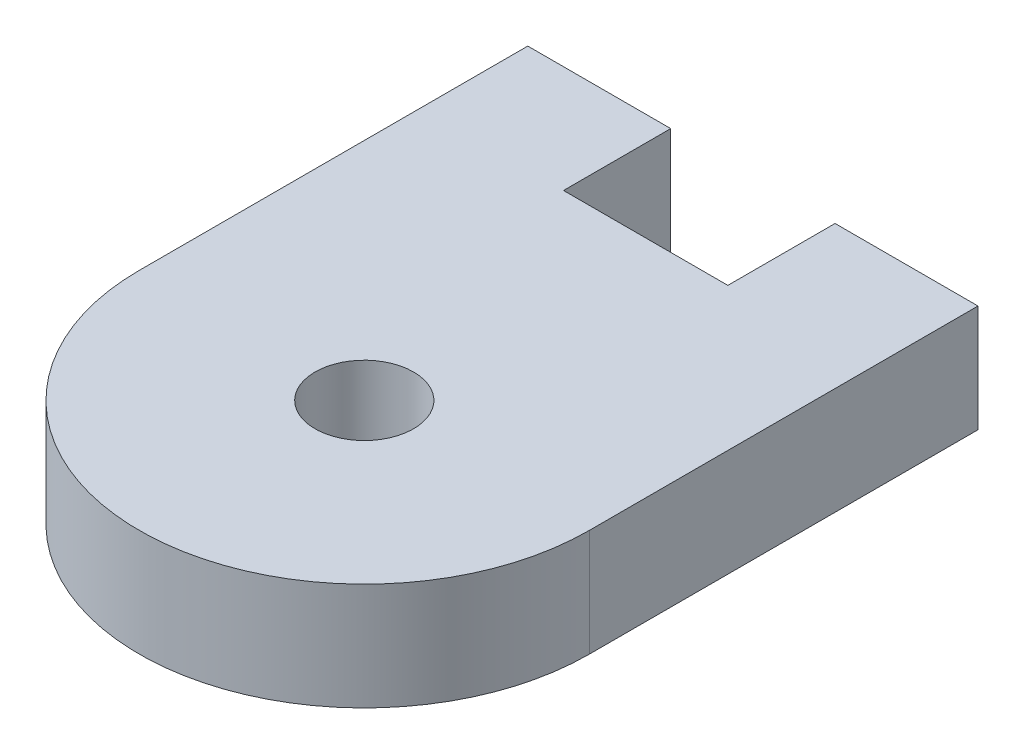
SolidWorks part; units mm, degrees
ref_plane "Front Plane" through (0, 0, 0) normal (0, 0, 1) x (1, 0, 0)
ref_plane "Top Plane" through (0, 0, 0) normal (0, 1, 0) x (1, 0, 0)
ref_plane "Right Plane" through (0, 0, 0) normal (1, 0, 0) x (0, 0, -1)
sketch "Sketch1" plane through (0, 0, 0) normal (0, 1, 0) x (1, 0, 0)
  line L1 (0, 0) -> (32, 0)
  line L2 (0, 0) -> (0, 20)
  line L3 (0, 20) -> (32, 20)
  line L4 (32, 0) -> (32, 20)
  arc A0 (0, 0) -> (32, 0) centre (16, 0) ccw
  dimension "D1" = 20
  dimension "D2" = 32
extrude "Boss-Extrude1" add sketch "Sketch1" along normal blind 7.62 contours L2 L3 L4 A0
sketch "Sketch2" plane through (0, 0, 0) normal (0, -1, 0) x (1, 0, 0)
  line L0 (32, 0) -> (0, 0) construction
  circle A0 centre (16, 0) radius 3.5
extrude "Cut-Extrude1" cut sketch "Sketch2" against normal through all
sketch "Sketch3" plane through (0, 0, -20) normal (0, 0, -1) x (-1, 0, 0)
  line L0 (0, 0) -> (-32, 0) construction
  line L1 (-32, 7.62) -> (-21.84, 7.62)
  line L2 (-32, 7.62) -> (-32, 0)
  line L3 (-32, 0) -> (-21.84, 0)
  line L4 (-21.84, 7.62) -> (-21.84, 0)
  line L6 (0, 7.62) -> (-10.16, 7.62)
  line L7 (0, 7.62) -> (0, 0)
  line L8 (0, 0) -> (-10.16, 0)
  line L9 (-10.16, 7.62) -> (-10.16, 0)
  dimension "D1" = 10.16
  dimension "D2" = 10.16
  dimension "D3" = 11.68
extrude "Boss-Extrude2" add sketch "Sketch3" along normal blind 7.62
equation "\"MDF\" = 0.3in"
equation "\"D1@Boss-Extrude1\"=\"MDF\""
equation "\"D1@Boss-Extrude2\"=\"MDF\""
